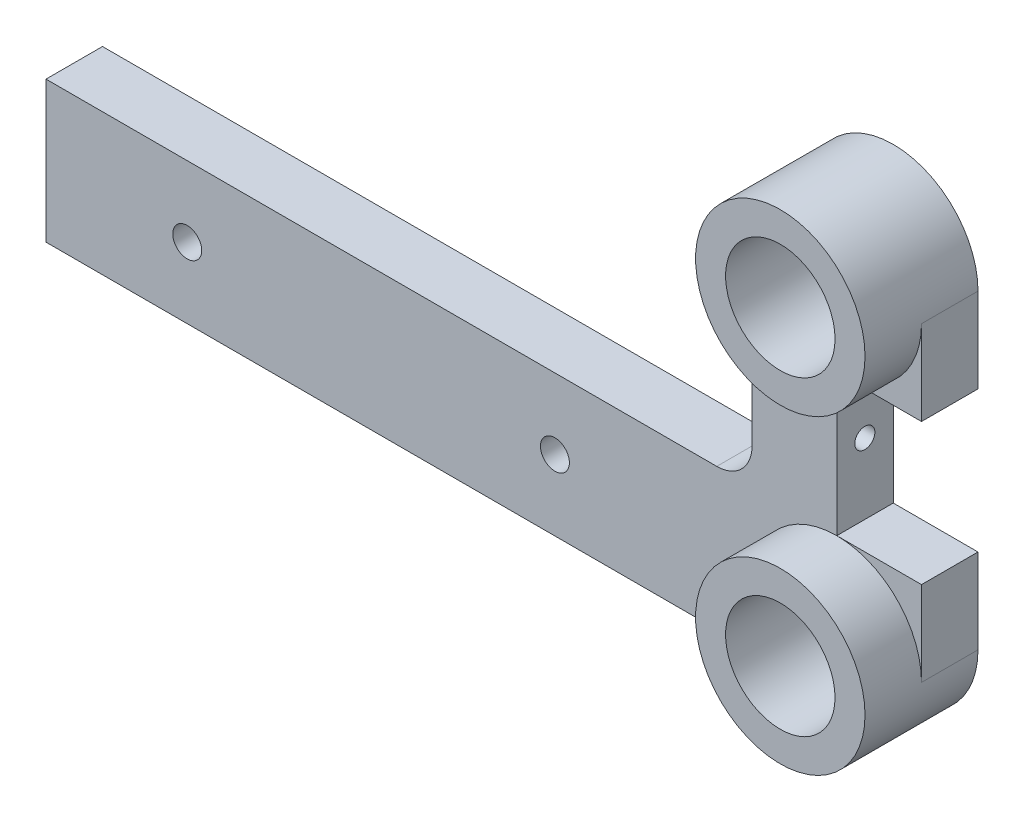
SolidWorks part; units mm, degrees
ref_plane "Plan de face" through (0, 0, 0) normal (0, 0, 1) x (1, 0, 0)
ref_plane "Plan de dessus" through (0, 0, 0) normal (0, 1, 0) x (1, 0, 0)
ref_plane "Plan de droite" through (0, 0, 0) normal (1, 0, 0) x (0, 0, -1)
ref_plane "Plan1" through (0, 0, 8) normal (0, 0, 1) x (1, 0, 0)
sketch "Esquisse1" plane through (0, 0, 8) normal (0, 0, 1) x (1, 0, 0)
  line L0 (-12, 44) -> (-12, 0)
  line L1 (12, 0) -> (12, 12)
  line L2 (12, 12) -> (0, 12)
  line L3 (0, 12) -> (0, 32)
  line L4 (0, 32) -> (12, 32)
  line L5 (12, 32) -> (12, 44)
  arc A0 (12, 44) -> (-12, 44) centre (0, 44) ccw
  arc A1 (-12, 0) -> (12, 0) centre (0, 0) ccw
extrude "Boss.-Extru.1" add sketch "Esquisse1" against normal blind 8
sketch "Esquisse2" plane through (-12, 0, 0) normal (-1, 0, 0) x (0, 0, 1)
  line L1 (0, 12) -> (8, 12)
  line L2 (0, 12) -> (0, -8)
  line L3 (0, -8) -> (8, -8)
  line L4 (8, 12) -> (8, -8)
  line L5 (8, -55) -> (8, 55) construction
  line L6 (0, 44) -> (0, 0) construction
  dimension "D1" = 20
extrude "Boss.-Extru.2" add sketch "Esquisse2" along normal blind 100 and the other way blind 5
sketch "Esquisse3" plane through (0, 0, 8) normal (0, 0, 1) x (1, 0, 0)
  circle A0 centre (0, 44) radius 12
extrude "Boss.-Extru.3" add sketch "Esquisse3" along normal blind 8
sketch "Esquisse4" plane through (0, 0, 8) normal (0, 0, 1) x (1, 0, 0)
  circle A0 centre (0, 0) radius 12
extrude "Boss.-Extru.4" add sketch "Esquisse4" along normal blind 8
hole_wizard "Diamètre du perçage Ø4.1 (4.1)1" positions "Esquisse6" profile "Esquisse5" hole size "Ø4.1" standard "Ansi Metric" end condition through all
sketch "Esquisse6" plane through (0, 0, 8) normal (0, 0, 1) x (1, 0, 0)
  line L0 (-92, 2) -> (-39.9238, 2) construction
  line L2 (-112, -8) -> (-112, 12) construction
  point P0 (-39.9238, 2)
  point P1 (-92, 2)
  point P12 (-65.9619, 2)
  point P13 (-112, 2)
  dimension "D1" = 52.0762
  dimension "D2" = 20
sketch "Esquisse5" plane through (-39.9238, 2, 8) normal (1, 0, 0) x (0, -1, 0)
  line L0 (0, 0) -> (0, 8)
  line L1 (0, 8) -> (2.05, 8)
  line L2 (2.05, 8) -> (2.05, 0)
  line L5 (2.05, 0) -> (0, 0)
  line L11 (0, -6.35) -> (0, 107.95) construction
  dimension "Diamètre du perçage jusqu'au prochain" = 4.1
  dimension "Profondeur du perçage jusqu'au prochain" = 8
hole_wizard "Diamètre du perçage Ø15.5 (15.5)1" positions "Esquisse8" profile "Esquisse7" hole size "Ø15.5" standard "Ansi Metric"
sketch "Esquisse8" plane through (0, 0, 16) normal (0, 0, 1) x (1, 0, 0)
  point P0 (0, 44)
  point P1 (0, 0)
sketch "Esquisse7" plane through (0, 44, 16) normal (1, 0, 0) x (0, -1, 0)
  line L0 (0, 0) -> (0, 16)
  line L1 (0, 16) -> (7.75, 16)
  line L2 (7.75, 16) -> (7.75, 0)
  line L5 (7.75, 0) -> (0, 0)
  line L11 (0, -6.35) -> (0, 107.95) construction
  dimension "Diamètre du perçage jusqu'au prochain" = 15.5
  dimension "Profondeur du perçage jusqu'au prochain" = 16
hole_wizard "Dégagement M2.51" positions "Esquisse10" profile "Esquisse9" hole size "M2.5" standard "Ansi Metric"
sketch "Esquisse10" plane through (0, 0, 0) normal (1, 0, 0) x (0, 0, -1)
  point P0 (-4.03, 22)
sketch "Esquisse9" plane through (0, 22, 4.03) normal (0, 1, 0) x (0, 0, -1)
  line L0 (0, 0) -> (0, 10)
  line L1 (0, 10) -> (1.425, 10)
  line L2 (1.425, 10) -> (1.425, 0)
  line L5 (1.425, 0) -> (0, 0)
  line L10 (0, 10) -> (-1.425, 10) construction
  line L11 (0, -6.35) -> (0, 107.95) construction
  dimension "Diamètre du perçage" = 2.85
  dimension "Profondeur du perçage" = 10
  dimension "Angle de pointe" = 180
fillet "Congé1" radius 5 2 edges at (-12, 12, 4) (-8.9443, -8, 4)
